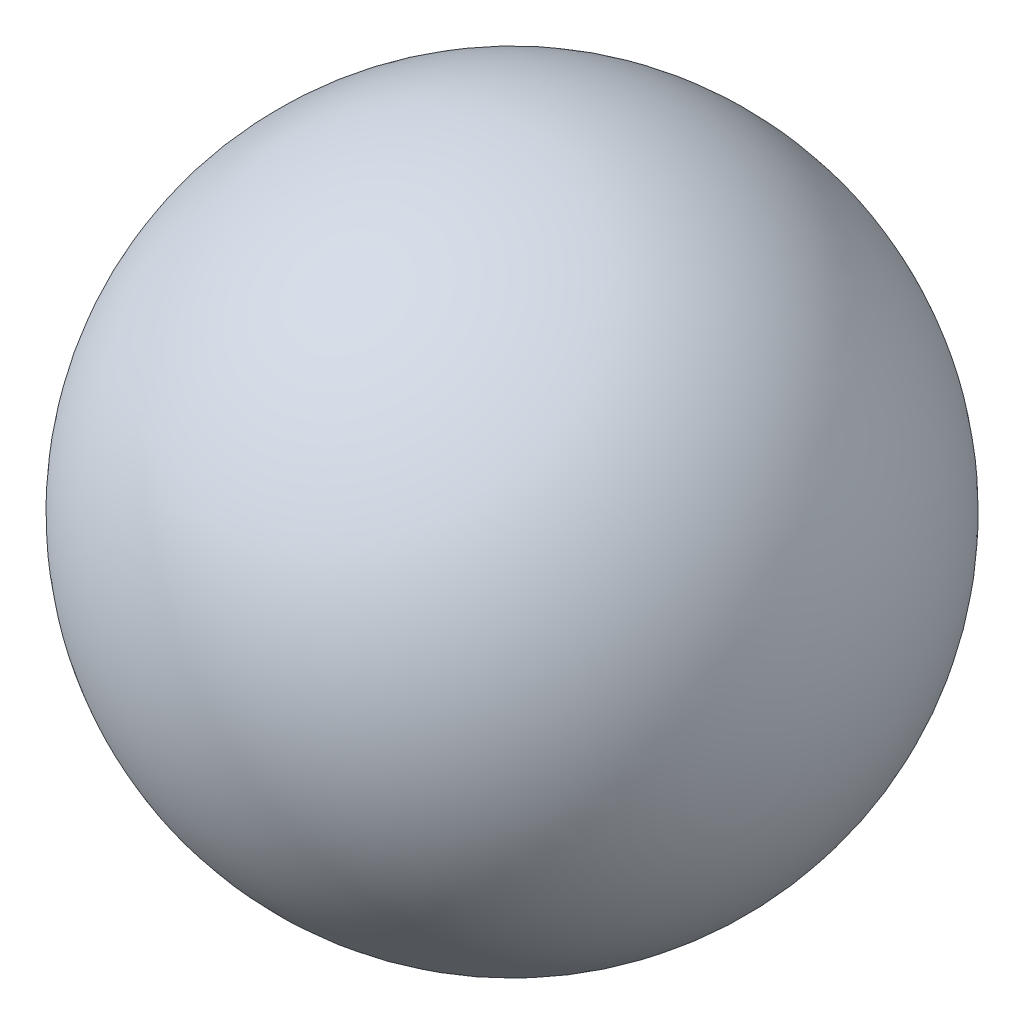
SolidWorks part; units mm, degrees
material "Chrome Stainless Steel"
ref_plane "Front Plane" through (0, 0, 0) normal (1, 0, 0) x (0, 1, 0)
ref_plane "Top Plane" through (0, 0, 0) normal (0, 0, 1) x (0, 1, 0)
ref_plane "Right Plane" through (0, 0, 0) normal (0, 1, 0) x (-1, 0, 0)
sketch "Sketch2" plane through (0, 0, 0) normal (1, 0, 0) x (0, 1, 0)
  line L0 (0, -9.525) -> (0, 9.525)
  arc A0 (0, 9.525) -> (0, -9.525) centre (0, 0) cw
  point P4 (0, 0)
  dimension "D1" = 19.05
revolve "Revolve1" add sketch "Sketch2" angle 360 about L0
equation "\"ball_diameter\"= 0.75in"
